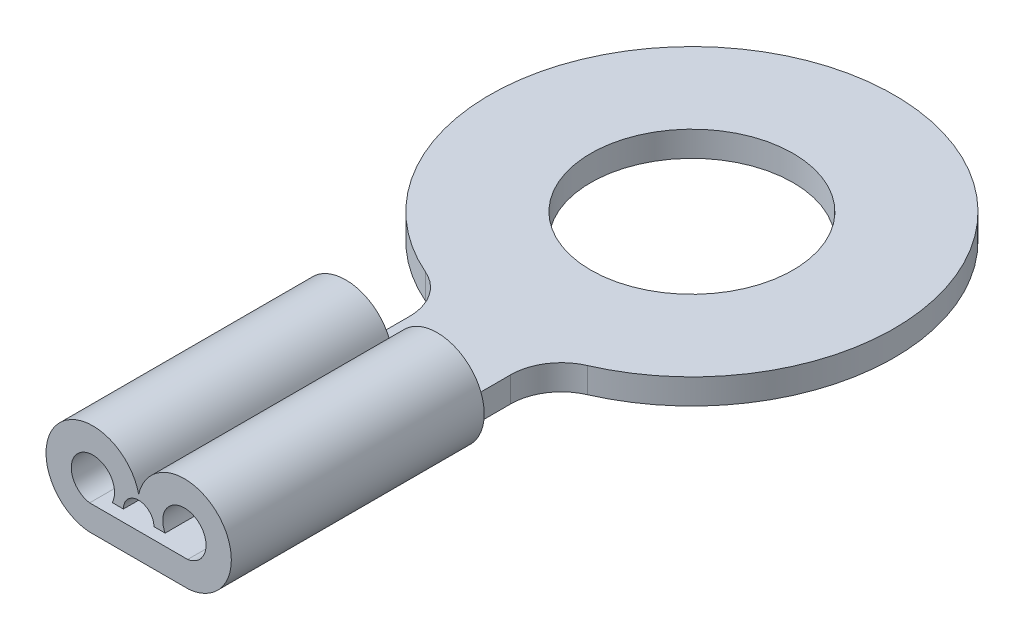
SolidWorks part; units mm, degrees
ref_plane "Plan de face" through (0, 0, 0) normal (0, 0, 1) x (1, 0, 0)
ref_plane "Plan de dessus" through (0, 0, 0) normal (0, 1, 0) x (1, 0, 0)
ref_plane "Plan de droite" through (0, 0, 0) normal (1, 0, 0) x (0, 0, -1)
sketch "Esquisse1" plane through (0, 0, 0) normal (0, 1, 0) x (1, 0, 0)
  line L0 (0, 0) -> (0, -10.9388) construction
  line L1 (-1, -10.9388) -> (1, -10.9388)
  line L3 (-1, -4.5826) -> (-1, -10.9388)
  line L5 (1, -4.5826) -> (1, -10.9388)
  circle A0 centre (0, 0) radius 2
  arc A1 (1.6, -3.6661) -> (-1.6, -3.6661) centre (0, 0) ccw
  circle A2 centre (0, 0) radius 4 construction
  arc A3 (-1.6, -3.6661) -> (-1, -4.5826) centre (-2, -4.5826) cw
  arc A4 (1.6, -3.6661) -> (1, -4.5826) centre (2, -4.5826) ccw
  dimension "D1" = 2
  dimension "D2" = 1
extrude "Extrusion1" add sketch "Esquisse1" along normal blind 0.5
sketch "Esquisse2" plane through (0, 0, 10.9388) normal (0, 0, 1) x (1, 0, 0)
  line L0 (-0.5234, 0.7279) -> (-0.302, 0.7279)
  line L1 (0.302, 0.7279) -> (0.5234, 0.7279)
  line L2 (0, 0) -> (0, -0.9889) construction
  line L3 (-0.9484, 0.4973) -> (0.9484, 0.4973)
  line L4 (1, 0) -> (-1, 0)
  arc A0 (-1, 0) -> (0, 1.1308) centre (-0.9043, 0.9229) cw
  arc A1 (-0.9484, 0.4973) -> (-0.5234, 0.7279) centre (-0.9043, 0.9229) cw
  arc A2 (-1, 0) -> (-0.0784, 0.5) centre (-0.9043, 0.9229) cw construction
  arc A3 (0.9484, 0.4973) -> (0.5234, 0.7279) centre (0.9043, 0.9229) ccw
  arc A4 (1, 0) -> (0, 1.1308) centre (0.9043, 0.9229) ccw
  arc A5 (0.302, 0.7279) -> (-0.302, 0.7279) centre (0, 0.7279) ccw
  dimension "D1" = 0.5
extrude "Extrusion2" add sketch "Esquisse2" against normal blind 5
